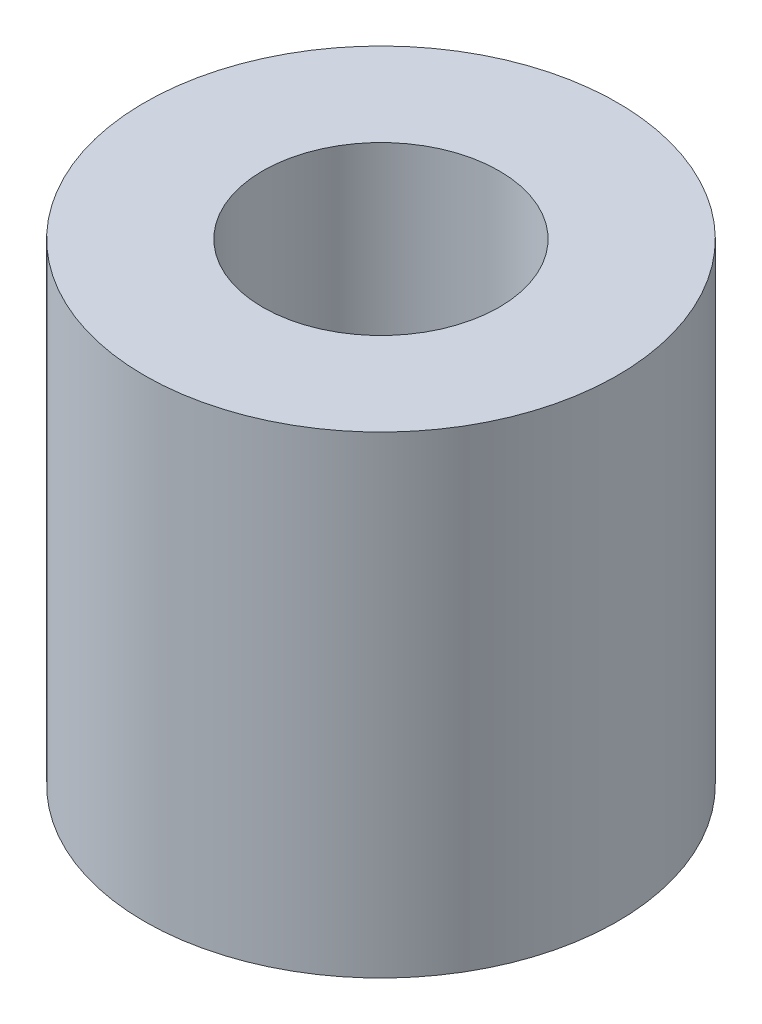
SolidWorks part; units mm, degrees
ref_plane "Front Plane" through (0, 0, 0) normal (0, 0, 1) x (1, 0, 0)
ref_plane "Top Plane" through (0, 0, 0) normal (0, 1, 0) x (1, 0, 0)
ref_plane "Right Plane" through (0, 0, 0) normal (1, 0, 0) x (0, 0, -1)
sketch "Sketch1" plane through (0, 0, 0) normal (0, 1, 0) x (1, 0, 0)
  circle A0 centre (0, 0) radius 6.35
  circle A1 centre (0, 0) radius 3.175
extrude "Boss-Extrude1" add sketch "Sketch1" along normal blind 12.7
